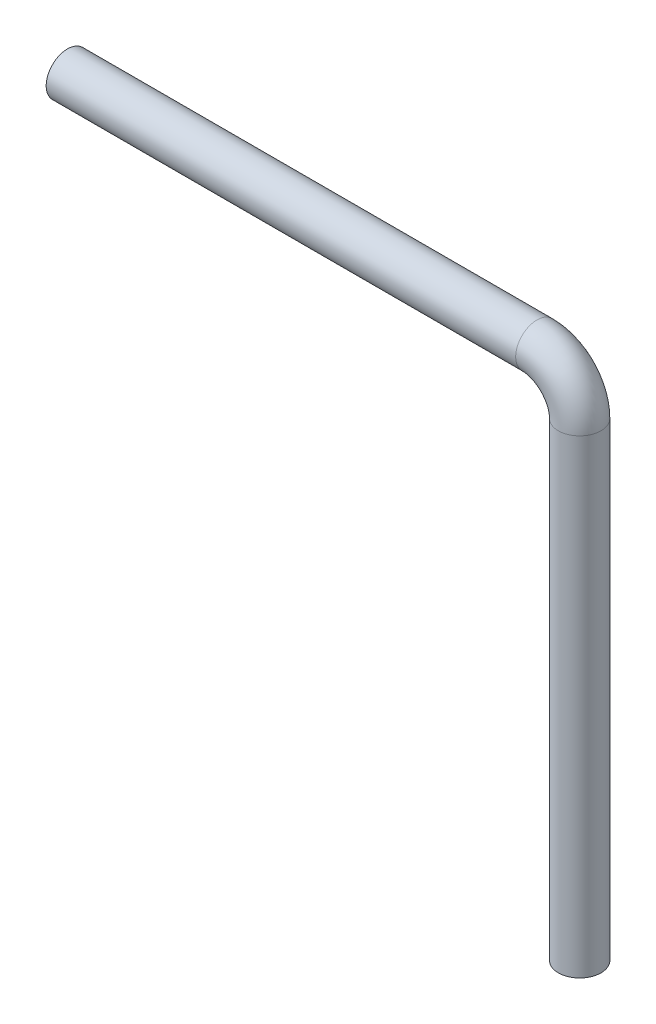
SolidWorks part; units mm, degrees
ref_plane "Front Plane" through (0, 0, 0) normal (0, 0, 1) x (1, 0, 0)
ref_plane "Top Plane" through (0, 0, 0) normal (0, 1, 0) x (1, 0, 0)
ref_plane "Right Plane" through (0, 0, 0) normal (1, 0, 0) x (0, 0, -1)
sketch "Sketch1" plane through (0, 0, 0) normal (0, 0, 1) x (1, 0, 0)
  line L0 (-120, 0) -> (-10, 0)
  line L1 (0, -10) -> (0, -120)
  arc A0 (-10, 0) -> (0, -10) centre (-10, -10) cw
  point P6 (0, 0)
  dimension "5" = 10
  dimension "D1" = 120
ref_plane "Plane1" through (0, -120, 0) normal (0, 1, 0) x (1, 0, 0)
sketch "Sketch2" plane through (0, -120, 0) normal (0, 1, 0) x (1, 0, 0)
  circle A0 centre (0, 0) radius 5
  dimension "D1" = 10
sweep "Sweep1" add profiles "Sketch2" path "Sketch1"
